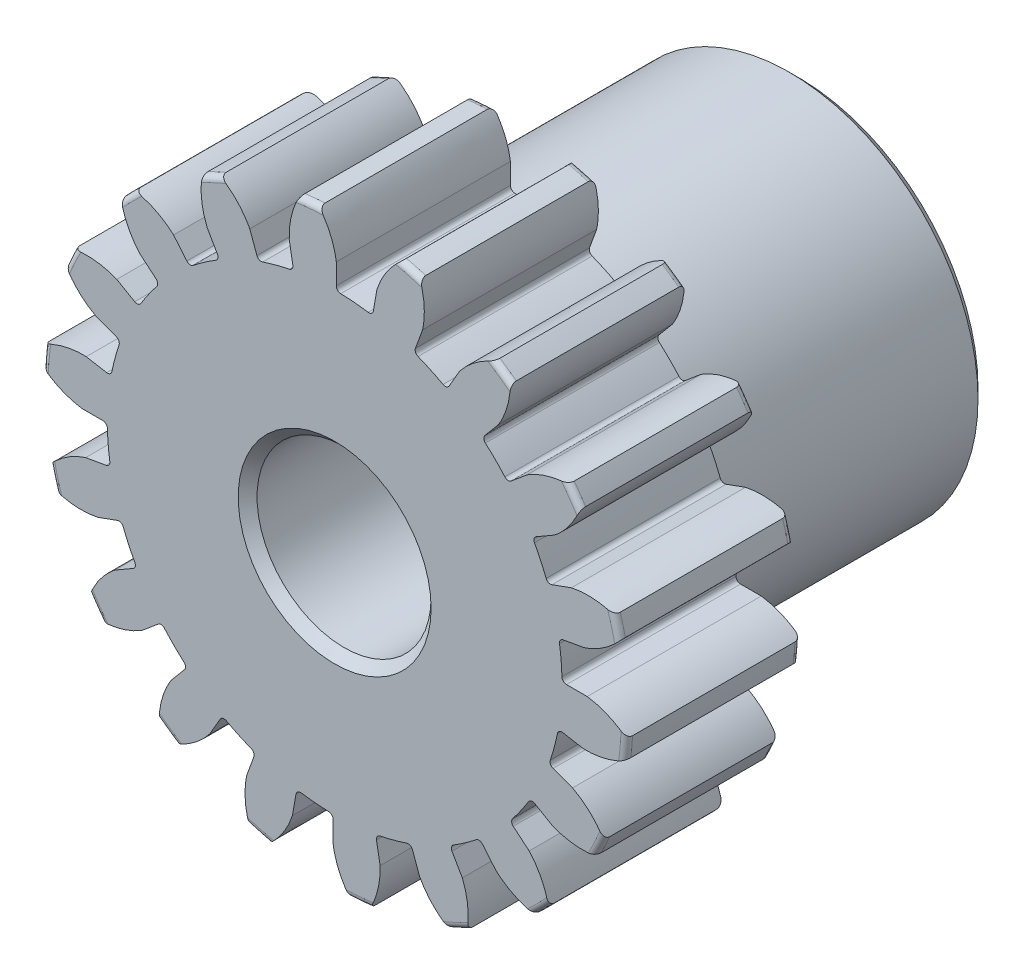
SolidWorks part; units mm, degrees
ref_plane "Front" through (0, 0, 0) normal (0, 0, 1) x (1, 0, 0)
ref_plane "Top" through (0, 0, 0) normal (0, 1, 0) x (1, 0, 0)
ref_plane "Right" through (0, 0, 0) normal (1, 0, 0) x (0, 0, -1)
sketch "Sketch1" plane through (0, 0, 0) normal (0, 0, 1) x (1, 0, 0)
  line L0 (-228.6, 0) -> (228.6, 0) construction
  circle A0 centre (0, 0) radius 8.001
  circle A1 centre (0, 0) radius 7.1374 construction
  circle A3 centre (0, 0) radius 6.2198 construction
  dimension "D1" = 0.9176
  dimension "OD" = 16.002
  dimension "Ptich Dia" = 14.2748
  dimension "D2" = 1.7812
  dimension "Root Dia" = 12.4397
  dimension "D3" = 0.8636
  dimension "Number of Teeth" = 457.2
extrude "Boss-Extrude1" add sketch "Sketch1" against normal blind 4.7625
sketch "Sketch2" plane through (0, 0, 0) normal (1, 0, 0) x (0, 0, -1)
  line L0 (4.7625, 0) -> (12.7, 0)
  line L1 (4.7625, 0) -> (4.7625, 5.1594)
  line L2 (4.7625, 5.1594) -> (12.7, 5.1594)
  line L3 (12.7, 5.1594) -> (12.7, 0)
  point P5 (12.7, -5.1594)
  dimension "Face Wd" = 4.7625
  dimension "D Oa'll Wd" = 12.7
  dimension "B Hub Dia" = 10.3187
revolve "Revolve1" add sketch "Sketch2" angle 360 about L0
fillet "Fillet2" radius 0.16 3 edges at (8.001, 0, -4.7625) (8.001, 0, 0) (5.1594, 0, -4.7625)
sketch "Sketch3" plane through (0, 0, 0) normal (0, 0, 1) x (1, 0, 0)
  line L0 (0, 0) -> (0, 8.001) construction
  line L1 (-1.7301, 6.69) -> (0, 7.1374)
  line L2 (-9.5921, 7.1374) -> (9.5921, 7.1374) construction
  line L3 (-9.2865, 4.7357) -> (9.2865, 9.5391) construction
  line L4 (-1.7301, 6.69) -> (0, 0) construction
  line L5 (-3.8403, 5.7446) -> (0, 0) construction
  line L6 (-3.8403, 5.7446) -> (-0.4444, 8.0148) construction
  line L7 (-1.2064, 6.8039) -> (0, 0) construction
  line L8 (-1.2064, 6.8039) -> (0.0253, 7.0223) construction
  arc A0 (-1.7301, 6.69) -> (-3.8403, 5.7446) centre (0, 0) ccw
  circle A1 centre (0, 0) radius 7.1374 construction
  circle A2 centre (0, 0) radius 6.9101 construction
  arc A3 (-1.7301, 6.69) -> (-1.2064, 6.8039) centre (0, 0) cw
  circle A4 centre (0, 0) radius 8.001 construction
  point P6 (0, 7.1374)
  dimension "D1" = 1.7871
  dimension "Pressure Angle" = 14.5
  dimension "D2" = 2.3232
  dimension "D3" = 4.0848
  dimension "D4" = 0.5361
  dimension "D5" = 1.2509
sketch "Sketch4" plane through (0, 0, 0) normal (0, 0, 1) x (1, 0, 0)
  line L0 (0, 0) -> (0.6197, 7.0832) construction
  line L1 (0.0439, 6.9099) -> (0.0439, 6.2197)
  line L2 (0, 7.1374) -> (1.2394, 7.029) construction
  line L3 (1.1567, 6.8126) -> (1.0368, 6.1328)
  line L4 (0.0439, 6.2197) -> (0, 0) construction
  line L5 (0, 0) -> (0, 8.001) construction
  arc A0 (1.0368, 6.1328) -> (0.0439, 6.2197) centre (0, 0) ccw
  arc A1 (0, 7.1374) -> (1.2394, 7.029) centre (0, 0) cw construction
  circle A2 centre (0, 0) radius 7.1374 construction
  circle A3 centre (0, 0) radius 6.9101 construction
  circle A4 centre (0, 0) radius 6.2198 construction
  arc A5 (1.8294, 7.8159) -> (-0.4444, 8.0148) centre (0, 0) ccw
  spline S0 degree 2 poles (-0.4444, 8.0148) (-0.0397, 7.5125) (0.0439, 6.9099) knots 0 0 0 1 1 1
  spline S1 degree 2 poles (1.8294, 7.8159) (1.3436, 7.3915) (1.1567, 6.8126) knots 0 0 0 1 1 1
  dimension "D1" = 1.2457
extrude "Cut-Extrude1" cut sketch "Sketch4" against normal through all
fillet "Fillet1" radius 0.1246 2 edges at (1.0368, 6.1328, -2.3812) (0.0439, 6.2197, -2.3812)
pattern_circular "CirPattern1" count 18 over 360 about axis through (0, 0, -4.7625) along (0, 0, 1) of "Cut-Extrude1", "Fillet1"
sketch "Sketch5" plane through (0, 0, 0) normal (0, 0, 1) x (1, 0, 0)
  circle A0 centre (0, 0) radius 2.3813
  circle A1 centre (0, 0) radius 4.7625 construction
  dimension "Bore Min" = 4.7625
  dimension "Bore Max" = 9.525
extrude "Cut-Extrude2" cut sketch "Sketch5" against normal through all
chamfer "Chamfer1" distance 0.258 angle 45 3 edges at (5.1594, 0, -12.7) (2.3813, 0, 0) (2.3813, 0, -12.7)
sketch "Pitch Dia" plane through (0, 0, 0) normal (0, 0, 1) x (1, 0, 0)
  circle A0 centre (0, 0) radius 7.1374 construction
  circle A1 centre (0, 0) radius 7.1374
equation "\"D1@Boss-Extrude1\" = \"Face Wd@Sketch2\""
equation "\"D2@Sketch3\" = \"D1@Sketch3\"*1.3"
equation "\"D3@Sketch3\" = \"D1@Sketch3\"+\"D2@Sketch3\"-.001"
equation "\"D4@Sketch3\" = \"D1@Sketch3\"*.3"
equation "\"D5@Sketch3\" = \"D1@Sketch3\"-\"D4@Sketch3\""
equation "\"D1@Sketch4\" = 1.5708/(\"Number of Teeth@Sketch1\"/\"Ptich Dia@Sketch1\")"
equation "\"D1@Chamfer1\" = \"B Hub Dia@Sketch2\"*.025"
equation "\"D1@CirPattern1\" = \"Number of Teeth@Sketch1\""
equation "\"D1@Fillet1\" = \"D1@Sketch4\"*.1"
equation "\"D1@Fillet2\" = \"OD@Sketch1\"*.01"
equation "\"D1@Sketch1\" = 1.157/(\"Number of Teeth@Sketch1\"/\"Ptich Dia@Sketch1\")"
